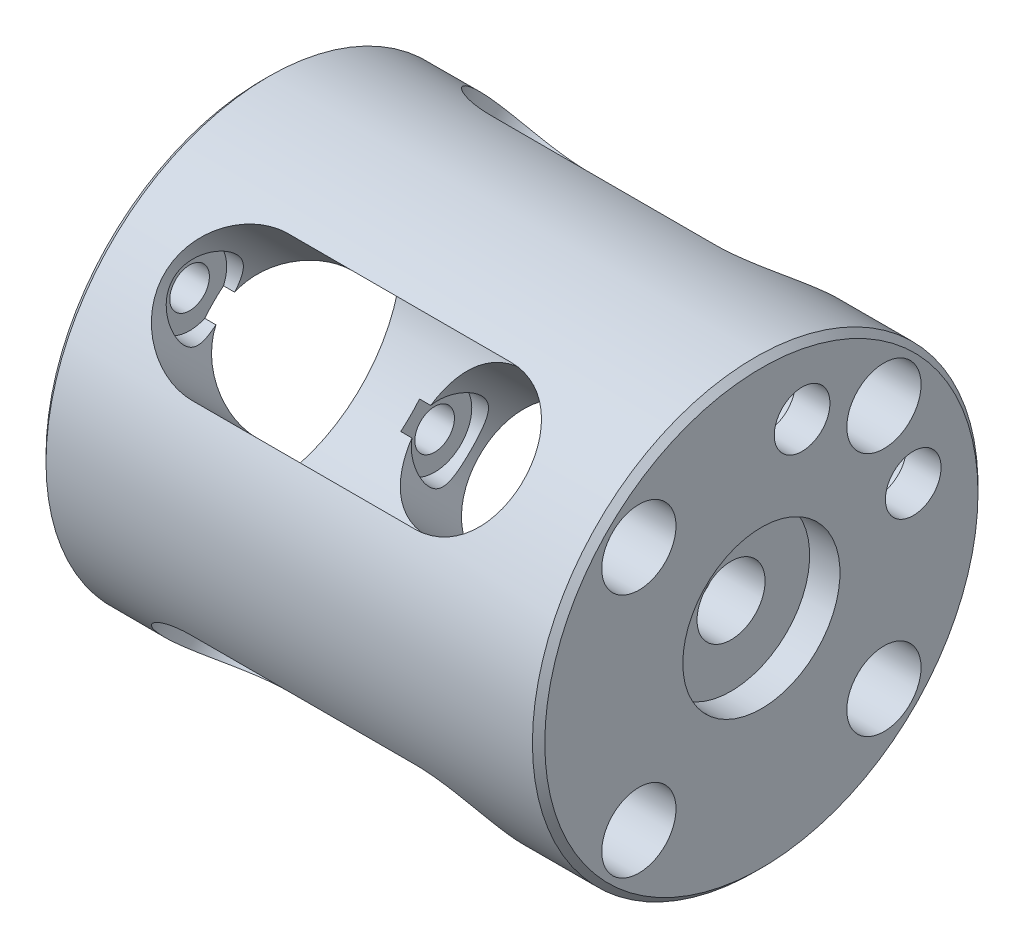
SolidWorks part; units mm, degrees
ref_plane "Front Plane" through (0, 0, 0) normal (0, 0, 1) x (1, 0, 0)
ref_plane "Top Plane" through (0, 0, 0) normal (0, 1, 0) x (1, 0, 0)
ref_plane "Right Plane" through (0, 0, 0) normal (1, 0, 0) x (0, 0, -1)
sketch "Sketch2" plane through (0, 0, 0) normal (0, 1, 0) x (1, 0, 0)
  line L0 (-68.5873, 0) -> (139.3492, 0) construction
  line L1 (-40.3, 18) -> (-40.3, 11.25)
  line L2 (0, 6.35) -> (-2.45, 6.35)
  line L3 (0, 6.35) -> (0, 18)
  line L4 (-2.45, 6.35) -> (-2.45, 2.75)
  line L5 (-2.45, 2.75) -> (-6.3, 2.75)
  line L6 (0, 18) -> (-40.3, 18)
  line L9 (-6.3, 2.75) -> (-6.3, 11.25)
  line L10 (-6.3, 11.25) -> (-40.3, 11.25)
  dimension "D1" = 18
  dimension "D2" = 2.45
  dimension "D3" = 2.75
  dimension "D4" = 6.3
  dimension "D5" = 6.35
  dimension "D6" = 11.25
  dimension "D7" = 34
revolve "Revolve1" add sketch "Sketch2" angle 360 about L0
sketch "Sketch7" plane through (0, 0, 0) normal (1, 0, 0) x (0, 0, -1)
  line L0 (-14.0397, -14.0397) -> (14.9167, 14.9167) construction
  line L1 (-15.1522, 15.1522) -> (16.849, -16.849) construction
  line L2 (-23.7673, 0) -> (22.3348, 0) construction
  circle A0 centre (-9.8995, 9.8995) radius 1.6
  circle A1 centre (9.8995, 9.8995) radius 1.6
  circle A2 centre (9.8995, -9.8995) radius 1.6
  circle A3 centre (-9.8995, -9.8995) radius 1.6
  dimension "D7" = 3.2
  dimension "D8" = 3.2
  dimension "D9" = 3.2
  dimension "D10" = 3.2
  dimension "D1" = 45
  dimension "D2" = 90
  dimension "D3" = 14
  dimension "D4" = 14
  dimension "D5" = 14
  dimension "D6" = 14
extrude "Cut-Extrude1" cut sketch "Sketch7" against normal through all
sketch "Sketch8" plane through (0, 0, 0) normal (1, 0, 0) x (0, 0, -1)
  circle A0 centre (-9.8995, 9.8995) radius 3
  circle A1 centre (9.8995, 9.8995) radius 3
  circle A2 centre (-9.8995, -9.8995) radius 3
  circle A3 centre (9.8995, -9.8995) radius 3
  dimension "D1" = 6
  dimension "D2" = 6
  dimension "D3" = 6
  dimension "D4" = 6
extrude "Cut-Extrude2" cut sketch "Sketch8" against normal blind 36.3
chamfer "Chamfer1" distance 0.5 angle 45 2 edges at (0, 0, 18) (-40.3, 0, 18)
sketch "Sketch12" plane through (0, 0, 0) normal (0, 1, 0) x (1, 0, 0)
  line L0 (0, 0) -> (-40.3, 0) construction
  line L1 (-40.3, 17.5) -> (-40.3, -17.5) construction
ref_plane "Plane1" through (0, 0, 0) normal (0, 0.7071, -0.7071) x (-1, 0, 0)
sketch "Sketch13" plane through (0, 0, 0) normal (0, 0.7071, -0.7071) x (-1, 0, 0)
  line L0 (12, 0) -> (30, 0) construction
  line L1 (0, 0) -> (40.3, 0) construction
  line L2 (12, 5.5) -> (30, 5.5)
  line L3 (12, -5.5) -> (30, -5.5)
  line L6 (0, 17.5) -> (0, -17.5) construction
  arc A0 (12, 5.5) -> (12, -5.5) centre (12, 0) ccw
  arc A1 (30, -5.5) -> (30, 5.5) centre (30, 0) ccw
  point P4 (21, 0)
  dimension "D3" = 5.5
  dimension "D1" = 18
  dimension "D2" = 12
extrude "Cut-Extrude5" cut sketch "Sketch13" against normal through all and the other way through all
ref_plane "Plane2" through (0, 0, 0) normal (0, -0.7071, -0.7071) x (-1, 0, 0)
sketch "Sketch14" plane through (0, 0, 0) normal (0, -0.7071, -0.7071) x (-1, 0, 0)
  line L0 (12, 0) -> (30, 0) construction
  line L1 (0, 0) -> (40.3, 0) construction
  line L2 (12, 5.5) -> (30, 5.5)
  line L3 (12, -5.5) -> (30, -5.5)
  line L5 (0, 17.5) -> (0, -17.5) construction
  arc A0 (12, 5.5) -> (12, -5.5) centre (12, 0) ccw
  arc A1 (30, -5.5) -> (30, 5.5) centre (30, 0) ccw
  point P4 (21, 0)
  dimension "D3" = 5.5
  dimension "D1" = 18
  dimension "D2" = 12
extrude "Cut-Extrude6" cut sketch "Sketch14" against normal through all and the other way through all
sketch "Sketch15" plane through (0, 0, 0) normal (1, 0, 0) x (0, 0, -1)
  line L0 (9.8995, 9.8995) -> (0, 0) construction
  line L1 (3.287, 12.2673) -> (0, 0) construction
  line L2 (0, 0) -> (12.2673, 3.287) construction
  line L3 (12.2673, 3.287) -> (3.287, 12.2673) construction
  circle A0 centre (3.287, 12.2673) radius 2.25
  circle A1 centre (12.2673, 3.287) radius 2.25
  point P8 (7.7771, 7.7771)
  dimension "D4" = 4.5
  dimension "D5" = 4.5
  dimension "D1" = 12.7
  dimension "D2" = 12.7
  dimension "D3" = 12.7
extrude "Cut-Extrude7" cut sketch "Sketch15" against normal through all
sketch "Sketch16" plane through (-40.3, 0, 0) normal (-1, 0, 0) x (0, 0, 1)
  circle A0 centre (-12.2673, 3.287) radius 3
  circle A1 centre (-3.287, 12.2673) radius 3
  dimension "D1" = 6
  dimension "D2" = 6
extrude "Cut-Extrude8" cut sketch "Sketch16" against normal blind 37.5
